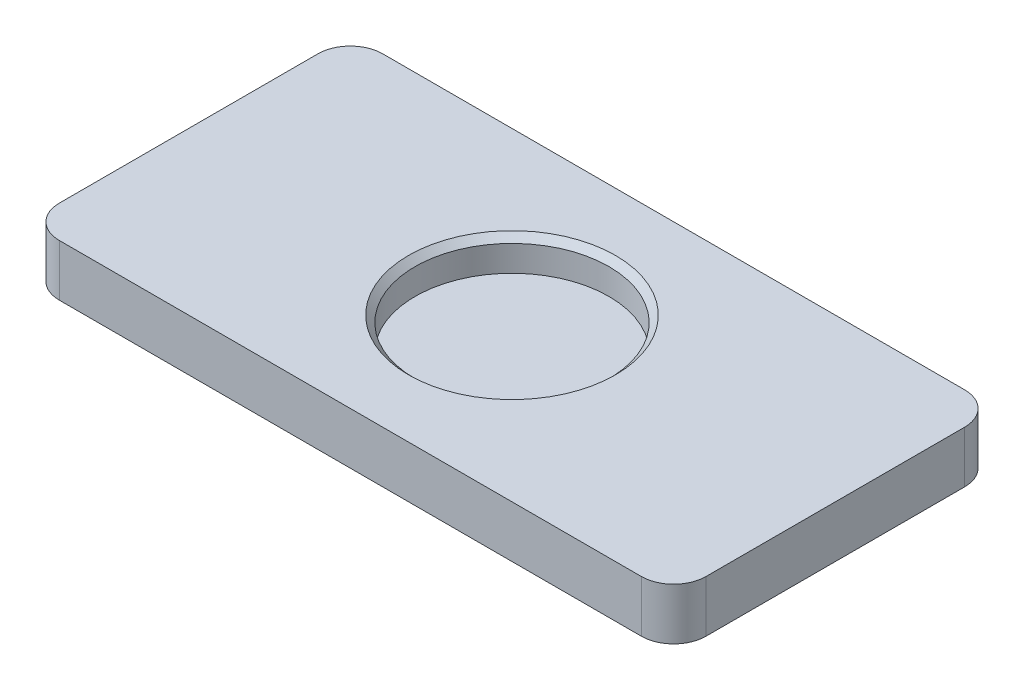
SolidWorks part; units mm, degrees
ref_plane "Front Plane" through (0, 0, 0) normal (0, 0, 1) x (1, 0, 0)
ref_plane "Top Plane" through (0, 0, 0) normal (0, 1, 0) x (1, 0, 0)
ref_plane "Right Plane" through (0, 0, 0) normal (1, 0, 0) x (0, 0, -1)
sketch "Sketch2" plane through (0, 0, 0) normal (0, 1, 0) x (1, 0, 0)
  line L1 (-25, 12.5) -> (25, 12.5)
  line L2 (-25, 12.5) -> (-25, -12.5)
  line L3 (-25, -12.5) -> (25, -12.5)
  line L4 (25, 12.5) -> (25, -12.5)
  line L5 (-25, 12.5) -> (25, -12.5) construction
  line L6 (-25, -12.5) -> (25, 12.5) construction
  point P0 (0, 0)
  dimension "D1" = 50
  dimension "D2" = 25
extrude "Boss-Extrude1" add sketch "Sketch2" along normal blind 4
fillet "Fillet1" radius 2.5 4 edges at (-25, 2, -12.5) (-25, 2, 12.5) (25, 2, -12.5) (25, 2, 12.5)
sketch "Sketch3" plane through (0, 4, 0) normal (0, 1, 0) x (1, 0, 0)
  circle A0 centre (0, 0) radius 7.5
  dimension "D1" = 15
extrude "Cut-Extrude1" cut sketch "Sketch3" against normal blind 2.5
chamfer "Chamfer1" distance 0.5 angle 45 1 edges at (0, 4, 7.5)
